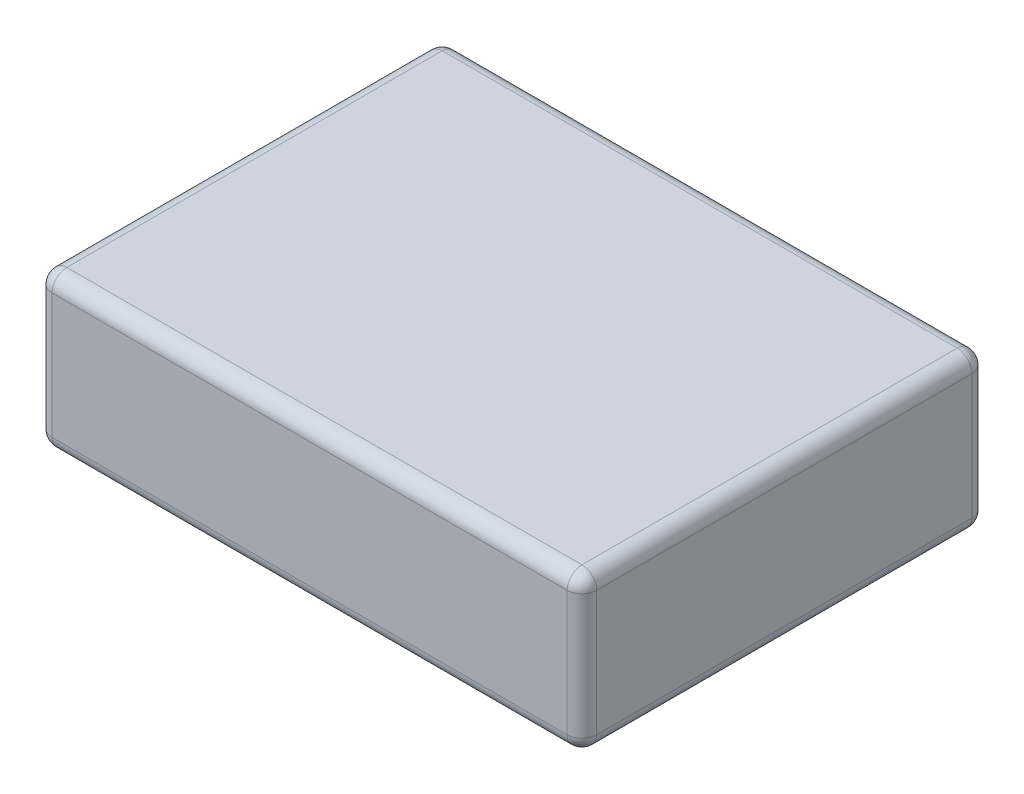
SolidWorks part; units mm, degrees
ref_plane "Front" through (0, 0, 0) normal (0, 0, 1) x (1, 0, 0)
ref_plane "Top" through (0, 0, 0) normal (0, 1, 0) x (1, 0, 0)
ref_plane "Right" through (0, 0, 0) normal (1, 0, 0) x (0, 0, -1)
sketch "Sketch1" plane through (0, 0, 0) normal (0, 1, 0) x (1, 0, 0)
  line L1 (0, 0) -> (93.98, 0)
  line L2 (0, 0) -> (0, 69.85)
  line L3 (0, 69.85) -> (93.98, 69.85)
  line L4 (93.98, 0) -> (93.98, 69.85)
  line L5 (0, 0) -> (93.98, 69.85) construction
  line L6 (0, 69.85) -> (93.98, 0) construction
  point P4 (46.99, 34.925)
  dimension "D1" = 69.85
  dimension "D2" = 93.98
extrude "Boss-Extrude1" add sketch "Sketch1" along normal blind 26.67
fillet "Fillet1" radius 2.54 12 edges at (93.98, 13.335, -69.85) (0, 13.335, -69.85) (0, 13.335, 0) (93.98, 13.335, 0) (46.99, 0, 0) (93.98, 0, -34.925) (46.99, 0, -69.85) (0, 0, -34.925) (46.99, 26.67, -69.85) (93.98, 26.67, -34.925) (46.99, 26.67, 0) (0, 26.67, -34.925)
